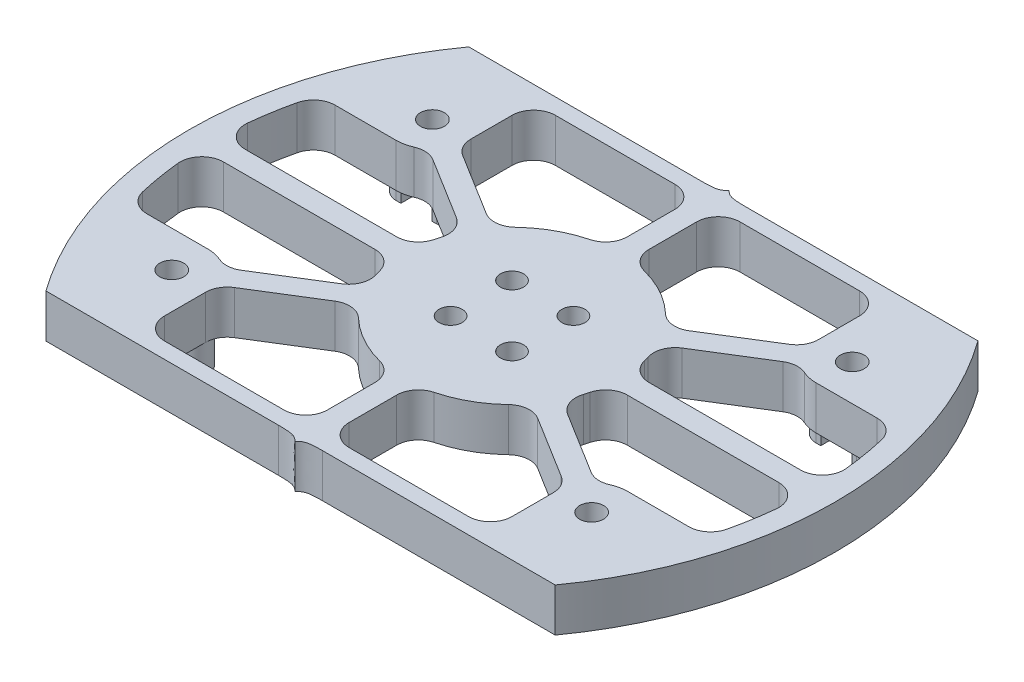
SolidWorks part; units mm, degrees
material "3.1355 (EN-AW 2024)"
ref_plane "Front" through (0, 0, 0) normal (0, 0, 1) x (1, 0, 0)
ref_plane "Top" through (0, 0, 0) normal (0, 1, 0) x (1, 0, 0)
ref_plane "Right" through (0, 0, 0) normal (1, 0, 0) x (0, 0, -1)
sketch "Эскиз1" plane through (0, 0, 0) normal (0, 1, 0) x (1, 0, 0)
  line L0 (0, 0) -> (0, 60) construction
  line L1 (0, 60) -> (10, 60) construction
  line L3 (79.1655, 0) -> (10, 0)
  line L4 (0, 30) -> (63.0426, 30) construction
  line L5 (10, 60) -> (79.1655, 60)
  line L6 (10, 0) -> (0, 0) construction
  line L7 (15.5828, 48) -> (73.5828, 48) construction
  line L8 (15.5828, 12) -> (73.5828, 12) construction
  line L9 (44.5828, 60) -> (44.5828, 0) construction
  arc A0 (10, 0) -> (10, 60) centre (50, 30) cw
  arc A1 (79.1655, 0) -> (79.1655, 60) centre (39.1655, 30) ccw
  point P5 (15.5828, 48)
  dimension "D3" = 50
  dimension "D1" = 60
  dimension "D2" = 12
  dimension "D4" = 38.84
  dimension "D5" = 58
extrude "Бобышка-Вытянуть1" add sketch "Эскиз1" along normal blind 6
sketch "Эскиз2" plane through (0, 6, 0) normal (0, 1, 0) x (1, 0, 0)
  line L4 (11.5292, 3) -> (77.6363, 3)
  line L5 (77.6363, 57) -> (11.5292, 57)
  line L6 (11.5292, 3) -> (77.6363, 3)
  line L7 (77.6363, 57) -> (11.5292, 57)
  arc A4 (11.5292, 57) -> (11.5292, 3) centre (50, 30) ccw
  arc A5 (77.6363, 3) -> (77.6363, 57) centre (39.1655, 30) ccw
  arc A6 (11.5292, 57) -> (11.5292, 3) centre (50, 30) ccw
  arc A7 (77.6363, 3) -> (77.6363, 57) centre (39.1655, 30) ccw
  dimension "D1" = 3
extrude "Вырез-Вытянуть1" cut sketch "Эскиз2" against normal through all
sketch "Эскиз3" plane through (0, 6, 0) normal (0, 1, 0) x (1, 0, 0)
  line L1 (89.1655, 30) -> (0, 30) construction
  circle A0 centre (15.5828, 48) radius 5
  circle A1 centre (73.5828, 48) radius 5
  arc A2 (79.1655, 0) -> (79.1655, 60) centre (39.1655, 30) ccw construction
  circle A3 centre (73.5828, 12) radius 5
  circle A4 centre (15.5828, 12) radius 5
  circle A5 centre (44.5828, 30) radius 15
  dimension "D1" = 10
  dimension "D2" = 10
  dimension "D3" = 30
extrude "Бобышка-Вытянуть2" add sketch "Эскиз3" against normal through all separate body
sketch "Эскиз4" plane through (0, 6, 0) normal (0, 1, 0) x (1, 0, 0)
  line L0 (77.6363, 57) -> (11.5292, 57) construction
  line L1 (11.5292, 3) -> (77.6363, 3) construction
  line L2 (77.6363, 57) -> (11.5292, 57) construction
  line L3 (11.5292, 3) -> (77.6363, 3) construction
  line L4 (44.5828, 45) -> (44.5828, 57) construction
  line L5 (31.8382, 37.9104) -> (19.831, 45.3632) construction
  line L6 (57.3274, 37.9104) -> (69.3346, 45.3632) construction
  line L7 (3, 30) -> (29.5828, 30) construction
  line L8 (86.1655, 30) -> (59.5828, 30) construction
  line L9 (57.3274, 22.0896) -> (69.3346, 14.6368) construction
  line L10 (31.8382, 22.0896) -> (19.831, 14.6368) construction
  line L11 (44.5828, 15) -> (44.5828, 3) construction
  line L12 (46.0828, 44.9248) -> (46.0828, 57)
  line L13 (32.6931, 39.1453) -> (20.4263, 46.7591)
  line L14 (58.0545, 36.5963) -> (70.3213, 44.2102)
  line L15 (56.4724, 20.8547) -> (68.7392, 13.2409)
  line L16 (43.0828, 15.0752) -> (43.0828, 3)
  line L17 (31.111, 23.4037) -> (18.8443, 15.7898)
  line L18 (43.0828, 44.9248) -> (43.0828, 57)
  line L19 (31.111, 36.5963) -> (18.8443, 44.2102)
  line L20 (56.4724, 39.1453) -> (68.7392, 46.7591)
  line L21 (58.0545, 23.4037) -> (70.3213, 15.7898)
  line L22 (46.0828, 15.0752) -> (46.0828, 3)
  line L23 (32.6931, 20.8547) -> (20.4263, 13.2409)
  line L24 (32.6292, 39.1849) -> (20.622, 46.6376) construction
  line L25 (31.0471, 36.636) -> (19.0399, 44.0887) construction
  line L26 (43.0828, 45) -> (43.0828, 57) construction
  line L27 (46.0828, 45) -> (46.0828, 57) construction
  line L28 (56.5363, 39.1849) -> (68.5435, 46.6376) construction
  line L29 (58.1184, 36.636) -> (70.1256, 44.0887) construction
  line L30 (58.1184, 23.364) -> (70.1256, 15.9113) construction
  line L31 (56.5363, 20.8151) -> (68.5435, 13.3624) construction
  line L32 (46.0828, 15) -> (46.0828, 3) construction
  line L33 (43.0828, 15) -> (43.0828, 3) construction
  line L34 (32.6292, 20.8151) -> (20.622, 13.3624) construction
  line L35 (31.0471, 23.364) -> (19.0399, 15.9113) construction
  line L36 (3.0239, 28.5) -> (29.658, 28.5)
  line L37 (86.1416, 31.5) -> (59.5076, 31.5)
  line L38 (3.0239, 31.5) -> (29.658, 31.5)
  line L39 (86.1416, 28.5) -> (59.5076, 28.5)
  line L40 (3, 31.5) -> (29.5828, 31.5) construction
  line L41 (3, 28.5) -> (29.5828, 28.5) construction
  line L42 (86.1655, 31.5) -> (59.5828, 31.5) construction
  line L43 (86.1655, 28.5) -> (59.5828, 28.5) construction
  line L44 (43.0828, 57) -> (46.0828, 57)
  line L45 (3.0239, 31.5) -> (2.4021, 31.5)
  line L46 (2.4021, 31.5) -> (2.4021, 28.5)
  line L47 (2.4021, 28.5) -> (3.0239, 28.5)
  line L48 (3.0239, 28.5) -> (2.938, 28.4918)
  line L49 (86.1416, 31.5) -> (86.6727, 31.5)
  line L50 (86.6727, 31.5) -> (86.6727, 28.5)
  line L51 (86.6727, 28.5) -> (86.1416, 28.5)
  line L52 (43.0828, 3) -> (46.0828, 3)
  arc A0 (11.5292, 57) -> (11.5292, 3) centre (50, 30) ccw construction
  circle A1 centre (44.5828, 30) radius 15
  arc A2 (43.0828, 15.0752) -> (46.0828, 15.0752) centre (44.5828, 30) ccw
  arc A3 (77.6363, 3) -> (77.6363, 57) centre (39.1655, 30) ccw construction
  arc A4 (11.5292, 57) -> (11.5292, 3) centre (50, 30) ccw construction
  arc A5 (77.6363, 3) -> (77.6363, 57) centre (39.1655, 30) ccw construction
  circle A6 centre (73.5828, 48) radius 5 construction
  circle A7 centre (73.5828, 12) radius 5 construction
  circle A8 centre (15.5828, 12) radius 5 construction
  circle A9 centre (15.5828, 48) radius 5 construction
  arc A10 (68.7392, 46.7591) -> (70.3213, 44.2102) centre (73.5828, 48) ccw
  arc A11 (70.3213, 15.7898) -> (68.7392, 13.2409) centre (73.5828, 12) ccw
  arc A12 (20.4263, 13.2409) -> (18.8443, 15.7898) centre (15.5828, 12) ccw
  arc A13 (18.8443, 44.2102) -> (20.4263, 46.7591) centre (15.5828, 48) ccw
  arc A14 (56.4724, 20.8547) -> (58.0545, 23.4037) centre (44.5828, 30) ccw
  arc A15 (31.111, 23.4037) -> (32.6931, 20.8547) centre (44.5828, 30) ccw
  arc A16 (59.5076, 28.5) -> (59.5076, 31.5) centre (44.5828, 30) ccw
  arc A17 (58.0545, 36.5963) -> (56.4724, 39.1453) centre (44.5828, 30) ccw
  arc A18 (29.658, 31.5) -> (29.658, 28.5) centre (44.5828, 30) ccw
  arc A19 (32.6931, 39.1453) -> (31.111, 36.5963) centre (44.5828, 30) ccw
  arc A20 (46.0828, 44.9248) -> (43.0828, 44.9248) centre (44.5828, 30) ccw
  circle M2 centre (44.5828, 30) radius 15
  dimension "D1" = 0
  dimension "D2" = 1.5
  dimension "D3" = 1.5
  dimension "D4" = 1.5
  dimension "D5" = 1.5
extrude "Бобышка-Вытянуть3" add sketch "Эскиз4" against normal through all contours A13 L19 L13 M2 | L44 L18 L12 M2 | A10 L20 L14 M2 | L51 L50 L49 L37 L39 M2 | A11 L21 L15 M2 | L16 L52 L22 M2 | A12 L23 L17 M2 | L46 L47 L36 L38 L45 M2
sketch "Эскиз5" plane through (0, 0, 0) normal (0, -1, 0) x (1, 0, 0)
  line L0 (20.5828, -3) -> (20.5828, -12)
  line L1 (11.5292, -3) -> (43.0828, -3) construction
  line L2 (44.5828, 0) -> (44.5828, -60) construction
  line L3 (0, -30) -> (89.1655, -30) construction
  line L4 (4.8336, -17) -> (15.5828, -17)
  line L5 (11.5292, -3) -> (20.5828, -3)
  line L6 (84.3319, -17) -> (73.5828, -17)
  line L7 (68.5828, -3) -> (68.5828, -12)
  line L8 (77.6363, -3) -> (68.5828, -3)
  line L9 (77.6363, -57) -> (68.5828, -57)
  line L10 (68.5828, -57) -> (68.5828, -48)
  line L11 (84.3319, -43) -> (73.5828, -43)
  line L12 (11.5292, -57) -> (20.5828, -57)
  line L13 (4.8336, -43) -> (15.5828, -43)
  line L14 (20.5828, -57) -> (20.5828, -48)
  arc A0 (79.1655, -60) -> (79.1655, 0) centre (39.1655, -30) ccw construction
  arc A1 (11.5292, -3) -> (3.0239, -28.5) centre (50, -30) ccw construction
  arc A3 (20.4263, -13.2409) -> (18.8443, -15.7898) centre (15.5828, -12) ccw construction
  arc A4 (11.5292, -3) -> (4.8336, -17) centre (50, -30) ccw
  arc A5 (20.5828, -12) -> (15.5828, -17) centre (15.5828, -12) ccw
  arc A6 (68.5828, -12) -> (73.5828, -17) centre (73.5828, -12) cw
  arc A7 (77.6363, -3) -> (84.3319, -17) centre (39.1655, -30) cw
  arc A8 (77.6363, -57) -> (84.3319, -43) centre (39.1655, -30) ccw
  arc A9 (68.5828, -48) -> (73.5828, -43) centre (73.5828, -48) ccw
  arc A10 (20.5828, -48) -> (15.5828, -43) centre (15.5828, -48) cw
  arc A11 (11.5292, -57) -> (4.8336, -43) centre (50, -30) cw
extrude "Бобышка-Вытянуть4" add sketch "Эскиз5" against normal through all
fillet "Скругление1" radius 3 40 edges at (70.3213, 3, -44.2102) (58.0545, 3, -36.5963) (59.5076, 3, -31.5) (59.5076, 3, -28.5) (58.0545, 3, -23.4037) (70.3213, 3, -15.7898) (84.3319, 3, -17) (86.1416, 3, -28.5) (86.1416, 3, -31.5) (84.3319, 3, -43) (56.4724, 3, -39.1453) (46.0828, 3, -44.9248) (46.0828, 3, -57) (68.5828, 3, -57) (68.7392, 3, -46.7591) (43.0828, 3, -44.9248) (43.0828, 3, -57) (20.5828, 3, -57) (32.6931, 3, -39.1453) (20.4263, 3, -46.7591) (31.111, 3, -36.5963) (18.8443, 3, -44.2102) (4.8336, 3, -43) (3.0239, 3, -31.5) (29.658, 3, -31.5) (29.658, 3, -28.5) (3.0239, 3, -28.5) (4.8336, 3, -17) (18.8443, 3, -15.7898) (31.111, 3, -23.4037) (43.0828, 3, -3) (20.5828, 3, -3) (20.4263, 3, -13.2409) (32.6931, 3, -20.8547) (43.0828, 3, -15.0752) (56.4724, 3, -20.8547) (46.0828, 3, -15.0752) (46.0828, 3, -3) (68.5828, 3, -3) (68.7392, 3, -13.2409)
sketch "Эскиз8" plane through (0, 0, 0) normal (0, -1, 0) x (1, 0, 0)
  line L0 (44.5828, 0) -> (44.5828, -60) construction
  line L1 (0, -30) -> (89.1655, -30) construction
  line L2 (9.4123, -0.8) -> (41.5278, -0.8)
  line L3 (79.1655, 0) -> (10, 0) construction
  line L4 (40.1307, -0.8) -> (42.9249, -0.8) construction
  line L5 (79.7532, -0.8) -> (47.6378, -0.8)
  line L6 (79.1655, 0) -> (10, 0)
  line L7 (79.1655, -60) -> (10, -60)
  line L8 (79.7532, -59.2) -> (47.6378, -59.2)
  line L9 (9.4123, -59.2) -> (41.5278, -59.2)
  arc A0 (79.1655, -60) -> (79.1655, 0) centre (39.1655, -30) ccw construction
  arc A1 (10, 0) -> (10, -60) centre (50, -30) ccw construction
  arc A2 (10, 0) -> (9.4123, -0.8) centre (50, -30) ccw
  arc A3 (79.7532, -0.8) -> (79.1655, 0) centre (39.1655, -30) ccw
  arc A4 (79.7532, -59.2) -> (79.1655, -60) centre (39.1655, -30) cw
  arc A5 (10, -60) -> (9.4123, -59.2) centre (50, -30) cw
  spline S0 degree 3 poles (44.5828, 0) (43.9591, -0.7036) (43.2742, -0.8) (41.5278, -0.8) knots 0 0 0 0 1 1 1 1
  spline S1 degree 3 poles (44.5828, 0) (45.2064, -0.7036) (45.8914, -0.8) (47.6378, -0.8) knots 0 0 0 0 1 1 1 1
  spline S2 degree 3 poles (44.5828, -60) (45.2064, -59.2964) (45.8914, -59.2) (47.6378, -59.2) knots 0 0 0 0 1 1 1 1
  spline S3 degree 3 poles (44.5828, -60) (43.9591, -59.2964) (43.2742, -59.2) (41.5278, -59.2) knots 0 0 0 0 1 1 1 1
  dimension "D1" = 0.8
extrude "Вырез-Вытянуть2" cut sketch "Эскиз8" against normal through all contours S0 L6 A2 L2 | L6 S1 L5 A3 | L7 S3 L9 A5 | S2 L7 A4 L8
hole_wizard "Отверстие обработанное метчиком M4x0.71" positions "Эскиз7" profile "Эскиз6" tap size "M4x0.7" standard "Ansi Metric" end condition through all
sketch "Эскиз7" plane through (0, 0, 0) normal (0, -1, 0) x (-1, 0, 0)
  point P0 (-15.5828, 12)
  point P3 (-73.5828, 12)
  point P6 (-73.5828, 48)
  point P9 (-15.5828, 48)
sketch "Эскиз6" plane through (15.5828, 0, -12) normal (1, 0, 0) x (0, 0, -1)
  line L0 (0, 0) -> (0, 6)
  line L1 (0, 6) -> (1.65, 6)
  line L2 (1.65, 6) -> (1.65, 0)
  line L5 (1.65, 0) -> (0, 0)
  line L11 (0, -6.35) -> (0, 107.95) construction
  dimension "Диаметр проходного сверла" = 3.3
  dimension "Глубина проходного сверла" = 6
cosmetic thread "Отверстие резьбы1" parameters "D2"=4
cosmetic thread "Отверстие резьбы2" parameters "D2"=4
cosmetic thread "Отверстие резьбы3" parameters "D2"=4
cosmetic thread "Отверстие резьбы4" parameters "D2"=4
cosmetic thread "Отверстие резьбы6" parameters "D2"=4
cosmetic thread "Отверстие резьбы7" parameters "D2"=4
sketch "Эскиз9" plane through (0, 0, 0) normal (0, 1, 0) x (1, 0, 0)
  line L0 (15.5828, 50.2) -> (15.5828, 45.8) construction
  line L1 (12.7828, 50.2) -> (18.3828, 50.2)
  line L2 (12.7828, 45.8) -> (18.3828, 45.8)
  line L3 (20.5828, 54) -> (20.5828, 48.3308) construction
  line L4 (0, 30) -> (89.1655, 30) construction
  line L5 (44.5828, 60) -> (44.5828, 0) construction
  line L6 (12.7828, 14.2) -> (18.3828, 14.2)
  line L7 (12.7828, 9.8) -> (18.3828, 9.8)
  line L8 (76.3828, 45.8) -> (70.7828, 45.8)
  line L9 (76.3828, 50.2) -> (70.7828, 50.2)
  line L10 (76.3828, 9.8) -> (70.7828, 9.8)
  line L11 (76.3828, 14.2) -> (70.7828, 14.2)
  arc A1 (18.3828, 50.2) -> (18.3828, 45.8) centre (18.3828, 48) cw
  arc A3 (12.7828, 50.2) -> (12.7828, 45.8) centre (12.7828, 48) ccw
  arc A4 (9.4123, 59.2) -> (9.4123, 0.8) centre (50, 30) ccw construction
  arc A5 (79.7532, 0.8) -> (79.7532, 59.2) centre (39.1655, 30) ccw construction
  arc A6 (18.3828, 9.8) -> (18.3828, 14.2) centre (18.3828, 12) ccw
  arc A7 (12.7828, 9.8) -> (12.7828, 14.2) centre (12.7828, 12) cw
  arc A8 (76.3828, 50.2) -> (76.3828, 45.8) centre (76.3828, 48) cw
  arc A9 (70.7828, 50.2) -> (70.7828, 45.8) centre (70.7828, 48) ccw
  arc A10 (76.3828, 9.8) -> (76.3828, 14.2) centre (76.3828, 12) ccw
  arc A11 (70.7828, 9.8) -> (70.7828, 14.2) centre (70.7828, 12) cw
  point P2 (15.5828, 48)
  dimension "D2" = 2.2
  dimension "D1" = 4.4
extrude "Бобышка-Вытянуть5" add sketch "Эскиз9" against normal blind 4
hole_wizard "Отверстие обработанное метчиком M4x0.72" positions "Эскиз11" profile "Эскиз10" tap size "M4x0.7" standard "Ansi Metric" end condition through all
sketch "Эскиз11" plane through (0, -4, 0) normal (0, -1, 0) x (-1, 0, 0)
  point P0 (-73.5828, 48)
  point P3 (-15.5828, 48)
  point P6 (-15.5828, 12)
  point P9 (-73.5828, 12)
sketch "Эскиз10" plane through (73.5828, -4, -48) normal (1, 0, 0) x (0, 0, -1)
  line L0 (0, 0) -> (0, 10)
  line L1 (0, 10) -> (1.65, 10)
  line L2 (1.65, 10) -> (1.65, 0)
  line L5 (1.65, 0) -> (0, 0)
  line L11 (0, -6.35) -> (0, 107.95) construction
  dimension "Диаметр проходного сверла" = 3.3
  dimension "Глубина проходного сверла" = 10
cosmetic thread "Отверстие резьбы9" parameters "D2"=4
cosmetic thread "Отверстие резьбы10" parameters "D2"=4
sketch "Эскиз12" plane through (0, 0, 0) normal (0, -1, 0) x (1, 0, 0)
  circle A0 centre (44.5828, -30) radius 6 construction
  point P2 (44.5828, -24)
  point P7 (48.8254, -25.7574)
  point P8 (50.5828, -30)
  point P9 (48.8254, -34.2426)
  point P10 (44.5828, -36)
  point P11 (40.3401, -34.2426)
  point P12 (38.5828, -30)
  point P13 (40.3401, -25.7574)
  point P14 (44.5828, -30)
  dimension "D1" = 12
  dimension "D2" = 8
hole_wizard "Цековка для винта с внутренним шестигранником M31" positions "Эскиз14" profile "Эскиз13" counterbore size "M3" standard "Ansi Metric" end condition through all
sketch "Эскиз14" plane through (0, 0, 0) normal (0, -1, 0) x (-1, 0, 0)
  point P0 (-40.3401, 25.7574)
  point P3 (-48.8254, 25.7574)
  point P6 (-48.8254, 34.2426)
  point P9 (-40.3401, 34.2426)
sketch "Эскиз13" plane through (40.3401, 0, -25.7574) normal (1, 0, 0) x (0, 0, -1)
  line L0 (0, 0) -> (0, 6)
  line L1 (0, 6) -> (1.6, 6)
  line L3 (1.6, 6) -> (1.6, 3)
  line L4 (1.6, 3) -> (3.25, 3)
  line L5 (3.25, 3) -> (3.25, 0)
  line L7 (3.25, 0) -> (0, 0)
  line L11 (0, -6.35) -> (0, 107.95) construction
  dimension "Диаметр сквозного отверстия" = 3.2
  dimension "Глубина сквозного отверстия" = 6
  dimension "Диаметр цековки" = 6.5
  dimension "Глубина цековки" = 3
sketch "Эскиз15" plane through (0, -4, 0) normal (0, -1, 0) x (1, 0, 0)
  line L0 (13.4328, -9.8) -> (13.4328, -50.2)
  line L1 (12.7828, -9.8) -> (18.3828, -9.8) construction
  line L2 (18.3828, -50.2) -> (12.7828, -50.2) construction
  line L3 (15.5828, -10.35) -> (15.5828, -13.65) construction
  line L4 (17.7328, -9.8) -> (17.7328, -50.2)
  line L5 (13.4328, -9.8) -> (17.7328, -9.8)
  line L6 (13.4328, -50.2) -> (17.7328, -50.2)
  line L7 (44.5828, -30) -> (44.5828, -60) construction
  line L8 (75.7328, -50.2) -> (71.4328, -50.2)
  line L9 (75.7328, -9.8) -> (71.4328, -9.8)
  line L10 (71.4328, -9.8) -> (71.4328, -50.2)
  line L11 (75.7328, -9.8) -> (75.7328, -50.2)
  circle A0 centre (15.5828, -12) radius 1.65 construction
  point P6 (13.9328, -12)
  point P22 (75.2328, -12)
  dimension "D1" = 0.5
extrude "Вырез-Вытянуть3" cut sketch "Эскиз15" against normal up to surface (4 mm away) up to face at (40.3401, 0, -29.0074)
sketch "Эскиз16" plane through (0, 0, 0) normal (0, -1, 0) x (1, 0, 0)
  line L0 (0, -30) -> (0, -59.2) construction
  line L1 (9.4123, -59.2) -> (0, -59.2) construction
  arc A0 (9.4123, -0.8) -> (9.4123, -59.2) centre (50, -30) ccw construction
equation "\"D2@Эскиз3\"=\"D1@Эскиз3\""
